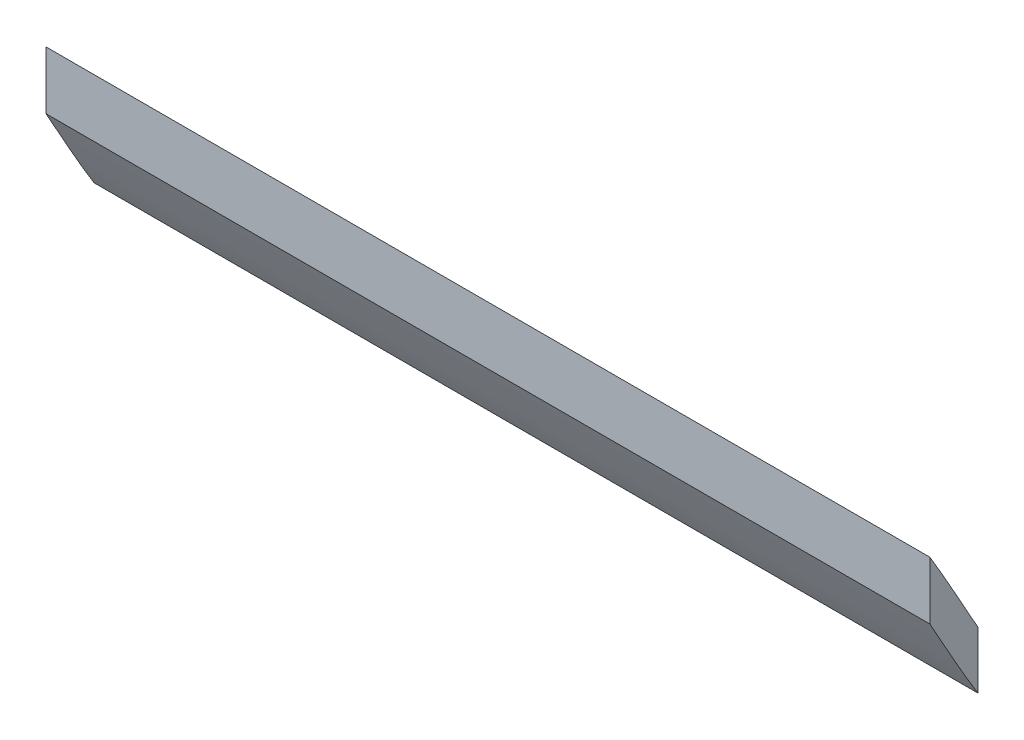
SolidWorks part; units mm, degrees
ref_plane "Front Plane" through (0, 0, 0) normal (0, 0, 1) x (1, 0, 0)
ref_plane "Top Plane" through (0, 0, 0) normal (0, 1, 0) x (1, 0, 0)
ref_plane "Right Plane" through (0, 0, 0) normal (1, 0, 0) x (0, 0, -1)
sketch "Sketch1" plane through (0, 0, 0) normal (1, 0, 0) x (0, 0, -1)
  line L4 (-94.2974, -47.1014) -> (-94.2974, -50.7051)
  line L5 (-91.2974, -52.3854) -> (-91.2974, -55.9318)
  spline S6 degree 3 poles (-91.2974, -52.3854) (-91.592, -51.8639) (-91.8832, -51.3401) (-92.8683, -49.5701) (-93.5622, -48.3236) (-94.2974, -47.1014) knots 0.684771 0.684771 0.684771 0.684771 0.75 0.75 0.905319 0.905319 0.905319 0.905319
  spline S7 degree 3 poles (-94.2974, -50.7051) (-93.6782, -51.8121) (-93.0679, -52.9244) (-92.0662, -54.6656) (-91.6892, -55.3032) (-91.2974, -55.9318) knots 0.106259 0.106259 0.106259 0.106259 0.25 0.25 0.333978 0.333978 0.333978 0.333978
  dimension "D2" = 3
extrude "Boss-Extrude1" add sketch "Sketch1" along normal blind 55
